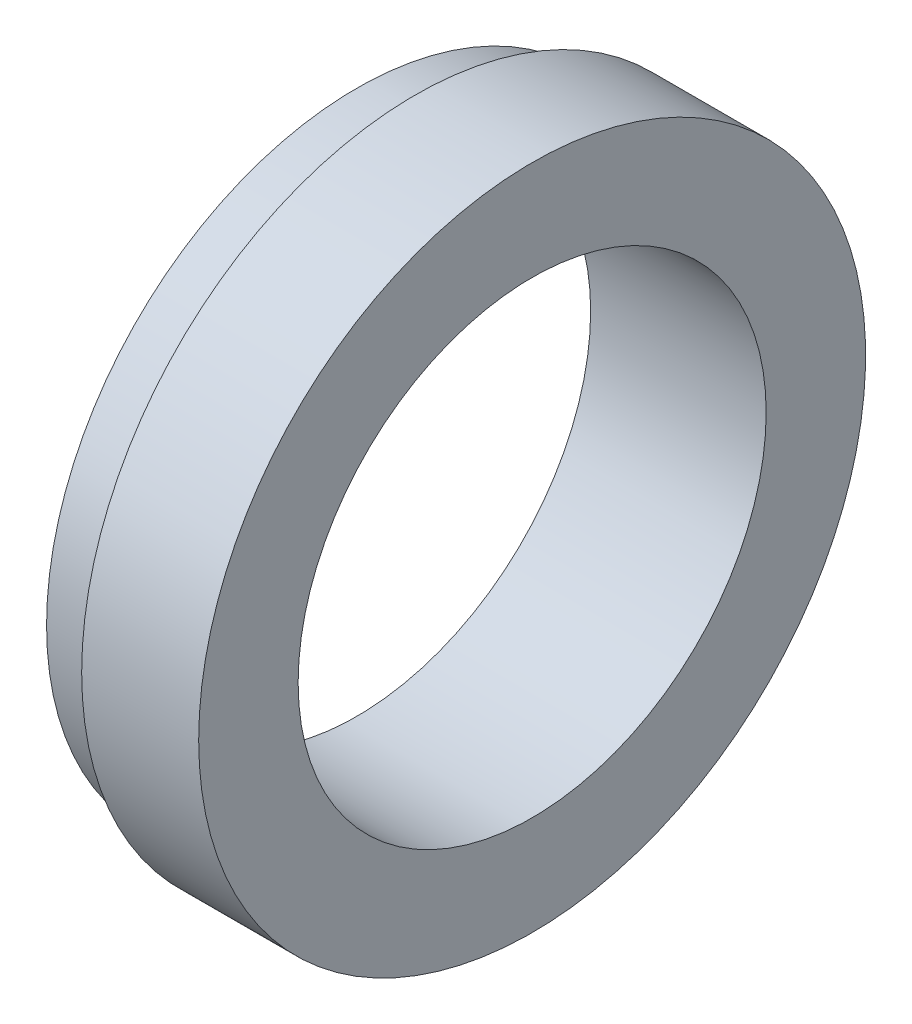
SolidWorks part; units mm, degrees
other "Исправление1"
sketch "Эскиз2" plane through (-5, 28.5, 28.5) normal (-0.9984, 0.0522, 0.0232) x (0.027, 0.0722, 0.997)
material "БрА9Мц2Л ГОСТ 493-79"
ref_plane "Спереди" through (0, 0, 0) normal (0, 0, 1) x (1, 0, 0)
ref_plane "Сверху" through (0, 0, 0) normal (0, 1, 0) x (1, 0, 0)
ref_plane "Справа" through (0, 0, 0) normal (1, 0, 0) x (0, 0, -1)
sketch "Эскиз1" plane through (0, 0, 0) normal (0, 0, 1) x (1, 0, 0)
  line L0 (10, -20) -> (10, -28.5)
  line L1 (10, -28.5) -> (0, -28.5)
  line L2 (0, -28.5) -> (0, -26.5)
  line L3 (0, -26.5) -> (-5, -26.5)
  line L4 (-5, -26.5) -> (-5, -20)
  line L5 (-5, -20) -> (10, -20)
  line L6 (0, 0) -> (38.561, 0) construction
  dimension "D1" = 57
  dimension "D2" = 40
  dimension "D3" = 53
  dimension "D4" = 15
  dimension "D5" = 5
revolve "Повернуть1" add sketch "Эскиз1" angle 360 about L6
